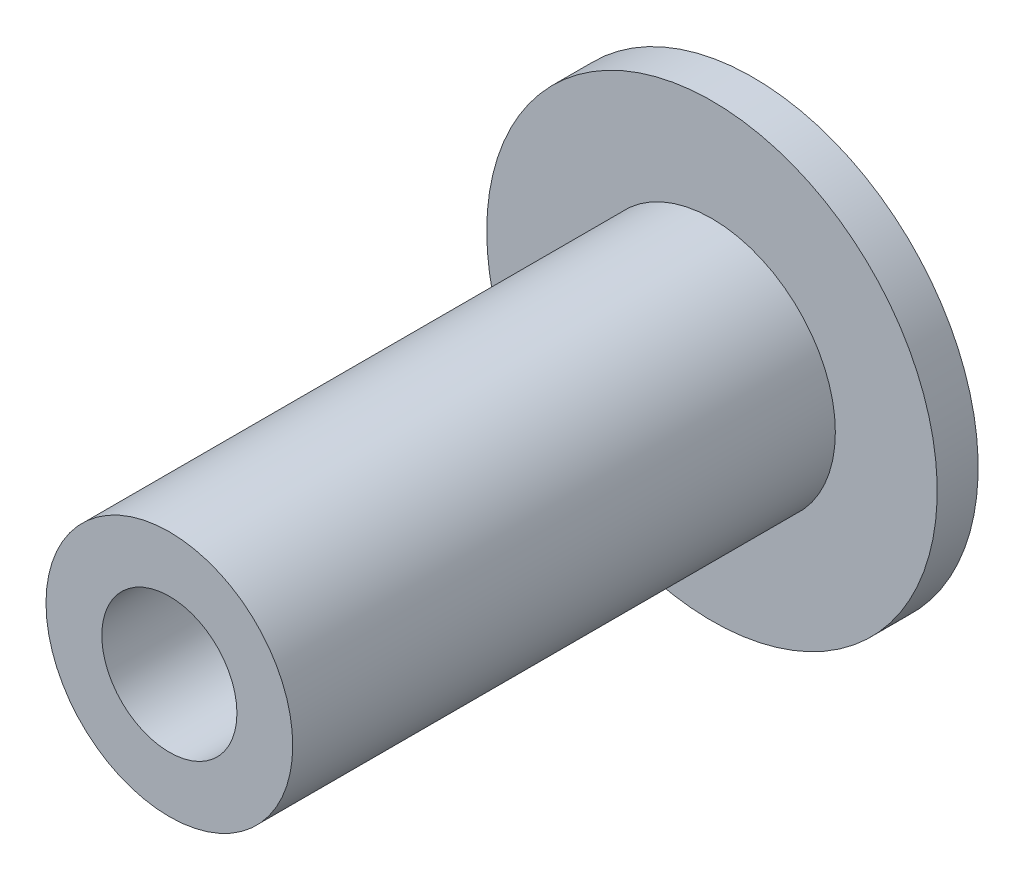
SolidWorks part; units mm, degrees
material "ABS"
ref_plane "Front Plane" through (0, 0, 0) normal (0, 0, 1) x (1, 0, 0)
ref_plane "Top Plane" through (0, 0, 0) normal (0, 1, 0) x (1, 0, 0)
ref_plane "Right Plane" through (0, 0, 0) normal (1, 0, 0) x (0, 0, -1)
sketch "Sketch1" plane through (0, 0, 0) normal (0, 0, 1) x (1, 0, 0)
  circle A0 centre (0, 0) radius 6.025
extrude "Boss-Extrude1" add sketch "Sketch1" along normal blind 10
sketch "Sketch2" plane through (0, 0, 10) normal (0, 0, 1) x (1, 0, 0)
  line L0 (0, -3.1496) -> (0, 3.1496) construction
  line L1 (2.7276, -1.5748) -> (-2.7276, 1.5748) construction
  line L2 (-2.7276, -1.5748) -> (2.7276, 1.5748) construction
  line L3 (0, 3.1496) -> (0.7493, 2.8395)
  line L4 (0.7493, 2.8395) -> (0.7846, 1.3589)
  line L5 (0.7846, 1.3589) -> (2.0845, 2.0687)
  line L6 (2.0845, 2.0687) -> (2.7276, 1.5748)
  line L7 (-1.9007, -3.2922) -> (2.1995, 3.8096) construction
  line L8 (2.7276, 1.5748) -> (2.8338, 0.7709)
  line L9 (2.8338, 0.7709) -> (1.5691, 0)
  line L10 (1.5691, 0) -> (2.8338, -0.7709)
  line L11 (2.8338, -0.7709) -> (2.7276, -1.5748)
  line L12 (2.7276, -1.5748) -> (2.0845, -2.0687)
  line L13 (2.0845, -2.0687) -> (0.7846, -1.3589)
  line L14 (0.7846, -1.3589) -> (0.7493, -2.8395)
  line L15 (0.7493, -2.8395) -> (0, -3.1496)
  line L16 (0, -3.1496) -> (-0.7493, -2.8395)
  line L17 (-0.7493, -2.8395) -> (-0.7846, -1.3589)
  line L18 (-0.7846, -1.3589) -> (-2.0845, -2.0687)
  line L19 (-2.0845, -2.0687) -> (-2.7276, -1.5748)
  line L20 (-2.7276, -1.5748) -> (-2.8338, -0.7709)
  line L21 (-2.8338, -0.7709) -> (-1.5691, 0)
  line L22 (-1.5691, 0) -> (-2.8338, 0.7709)
  line L23 (-2.8338, 0.7709) -> (-2.7276, 1.5748)
  line L24 (-2.7276, 1.5748) -> (-2.0845, 2.0687)
  line L25 (-2.0845, 2.0687) -> (-0.7846, 1.3589)
  line L26 (-0.7846, 1.3589) -> (-0.7493, 2.8395)
  line L27 (-0.7493, 2.8395) -> (0, 3.1496)
  circle A0 centre (0, 0) radius 3.1496
  point P7 (0, 0)
  point P9 (0, 0)
  point P12 (0, 0)
  point P18 (0, 0)
  point P45 (0, 0)
  dimension "D1" = 60
  dimension "D4" = 6.2992
  dimension "D2" = 60
  dimension "D3" = 1.7907
  dimension "D5" = 150
  dimension "D6" = 6
  dimension "D7" = 1.4986
extrude "Cut-Extrude1" [suppressed] cut sketch "Sketch2" against normal blind 10 contours L27 L26 L25 L24 L23 L22 L21 L20 L19 L18 L17 L16 L15 L14 L13 L12 L11 L10 L9 L8 L6 L5 L4 L3
sketch "Sketch3" plane through (0, 0, 10) normal (0, 0, 1) x (1, 0, 0)
  circle A0 centre (0, 0) radius 6.025
extrude "Boss-Extrude2" add sketch "Sketch3" along normal blind 16.5
sketch "Sketch4" plane through (0, 0, 26.5) normal (0, 0, 1) x (1, 0, 0)
  circle A0 centre (0, 0) radius 3.1496
extrude "Cut-Extrude2" [suppressed] cut sketch "Sketch4" against normal blind 16.5
sketch "Sketch5" plane through (0, 0, 0) normal (0, 0, -1) x (-1, 0, 0)
  circle A0 centre (0, 0) radius 11
extrude "Boss-Extrude3" add sketch "Sketch5" along normal blind 2
sketch "Sketch6" plane through (0, 0, 26.5) normal (0, 0, 1) x (1, 0, 0)
  circle A0 centre (0, 0) radius 3.3
extrude "Cut-Extrude3" cut sketch "Sketch6" against normal through all
